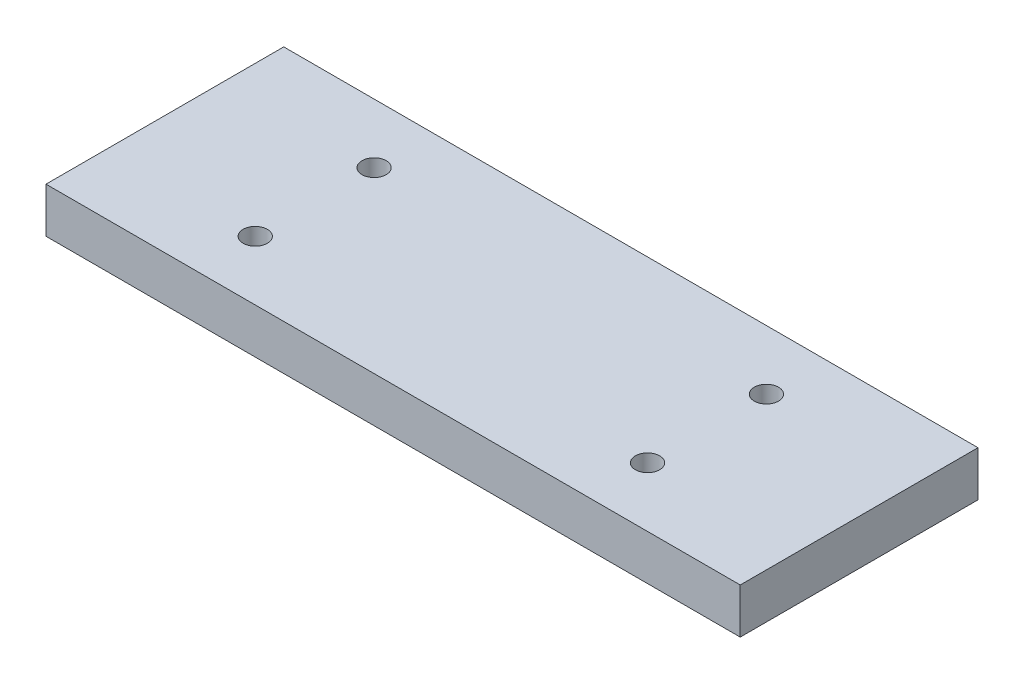
SolidWorks part; units mm, degrees
ref_plane "Piano frontale" through (0, 0, 0) normal (0, 0, 1) x (1, 0, 0)
ref_plane "Piano superiore" through (0, 0, 0) normal (0, 1, 0) x (1, 0, 0)
ref_plane "Piano destro" through (0, 0, 0) normal (1, 0, 0) x (0, 0, -1)
sketch "Schizzo1" plane through (0, 0, 0) normal (0, 1, 0) x (1, 0, 0)
  line L1 (-146, 50) -> (146, 50)
  line L2 (-146, 50) -> (-146, -50)
  line L3 (-146, -50) -> (146, -50)
  line L4 (146, 50) -> (146, -50)
  line L5 (-146, 50) -> (146, -50) construction
  line L6 (-146, -50) -> (146, 50) construction
  point P0 (0, 0)
  dimension "D1" = 292
  dimension "D2" = 100
extrude "Estrusione-Estrusione1" add sketch "Schizzo1" along normal blind 19
sketch "Schizzo3" plane through (0, 19, 0) normal (0, 1, 0) x (1, 0, 0)
  line L0 (-146, 50) -> (-146, -50) construction
  line L1 (-83, 25) -> (82, 25) construction
  line L2 (-83, 25) -> (-83, -25) construction
  line L3 (-83, -25) -> (82, -25) construction
  line L4 (82, 25) -> (82, -25) construction
  line L5 (146, 50) -> (-146, 50) construction
  dimension "D1" = 63
  dimension "D2" = 165
  dimension "D3" = 50
  dimension "D4" = 25
hole_wizard "Foro filettato M12-1" positions "Schizzo3D1" profile "Schizzo5" tap size "M12" standard "ISO" end condition through all
sketch3d "Schizzo3D1"
  point P0 (-83, 19, -25)
  point P3 (82, 19, -25)
  point P6 (82, 19, 25)
  point P9 (-83, 19, 25)
sketch "Schizzo5" plane through (-83, 19, -25) normal (1, 0, 0) x (0, 0, 1)
  line L0 (0, 0) -> (0, 19)
  line L1 (0, 19) -> (5.1, 19)
  line L2 (5.1, 19) -> (5.1, 0)
  line L5 (5.1, 0) -> (0, 0)
  line L11 (0, -6.35) -> (0, 107.95) construction
  dimension "Thru Tap Drill Dia." = 10.2
  dimension "Thru Tap Drill Depth" = 19
cosmetic thread "Filettatura del foro1"
cosmetic thread "Filettatura del foro2"
cosmetic thread "Filettatura del foro3"
cosmetic thread "Filettatura del foro4"
